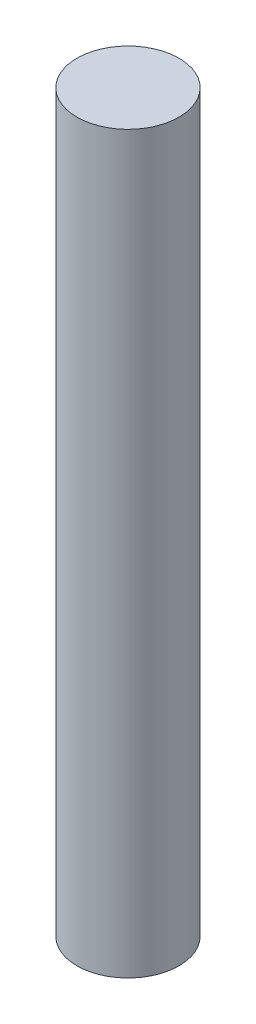
SolidWorks part; units mm, degrees
ref_plane "Front Plane" through (0, 0, 0) normal (0, 0, 1) x (1, 0, 0)
ref_plane "Top Plane" through (0, 0, 0) normal (0, 1, 0) x (1, 0, 0)
ref_plane "Right Plane" through (0, 0, 0) normal (1, 0, 0) x (0, 0, -1)
sketch "Sketch1" plane through (0, 0, 0) normal (0, 1, 0) x (1, 0, 0)
  circle A0 centre (0, 0) radius 3.175
  dimension "D1" = 6.35
extrude "Boss-Extrude1" add sketch "Sketch1" along normal blind 45.72
